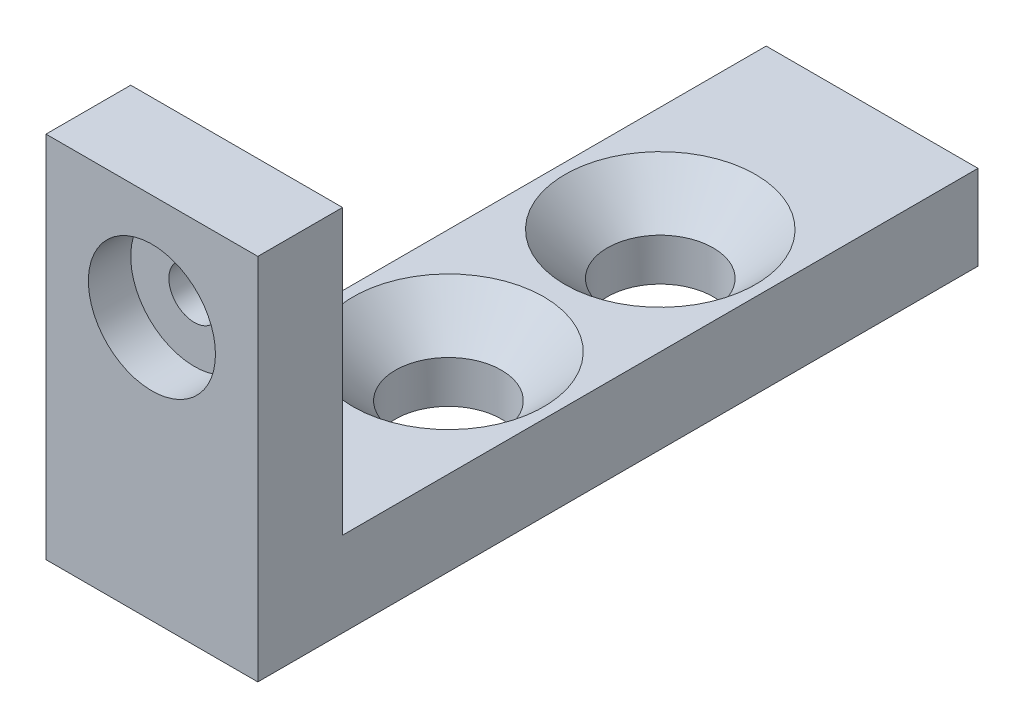
SolidWorks part; units mm, degrees
ref_plane "Front" through (0, 0, 0) normal (0, 0, 1) x (1, 0, 0)
ref_plane "Top" through (0, 0, 0) normal (0, 1, 0) x (1, 0, 0)
ref_plane "Right" through (0, 0, 0) normal (1, 0, 0) x (0, 0, -1)
sketch "Sketch1" plane through (0, 0, 0) normal (0, 0, 1) x (1, 0, 0)
  line L19 (2.5, 2.5) -> (-2.5, 2.5)
  line L20 (2.5, 2.5) -> (2.5, -6.2)
  line L21 (2.5, -6.2) -> (-2.5, -6.2)
  line L22 (-2.5, 2.5) -> (-2.5, -6.2)
extrude "Boss-Extrude2" add sketch "Sketch1" along normal blind 2 contours L19 L22 L21 L20
sketch "Sketch2" plane through (0, 0, 2) normal (0, 0, 1) x (1, 0, 0)
  circle A0 centre (0, 0) radius 1.5
extrude "Cut-Extrude1" cut sketch "Sketch2" against normal blind 1
sketch "Sketch3" plane through (0, 0, 1) normal (0, 0, 1) x (1, 0, 0)
  circle A0 centre (0, 0) radius 0.6
extrude "Cut-Extrude2" cut sketch "Sketch3" against normal blind 1
sketch "Sketch4" plane through (0, 0, 0) normal (0, 0, -1) x (-1, 0, 0)
  line L1 (-2.5, 2.5) -> (-2.5, -6.2) construction
  line L2 (-2.5, -4.2) -> (2.5, -4.2)
  line L7 (-2.5, -4.2) -> (-2.5, -6.2)
  line L8 (-2.5, -6.2) -> (2.5, -6.2)
  line L9 (2.5, -4.2) -> (2.5, -6.2)
extrude "Boss-Extrude4" add sketch "Sketch4" along normal blind 15
sketch "Sketch6" plane through (0, -4.2, 0) normal (0, 1, 0) x (1, 0, 0)
  circle A0 centre (0, 10) radius 1.25
  circle A1 centre (0, 5) radius 1.25
extrude "Cut-Extrude4" cut sketch "Sketch6" against normal blind 2
chamfer "Chamfer1" distance 1 angle 45 2 edges at (0, -4.2, -3.75) (0, -4.2, -8.75)
